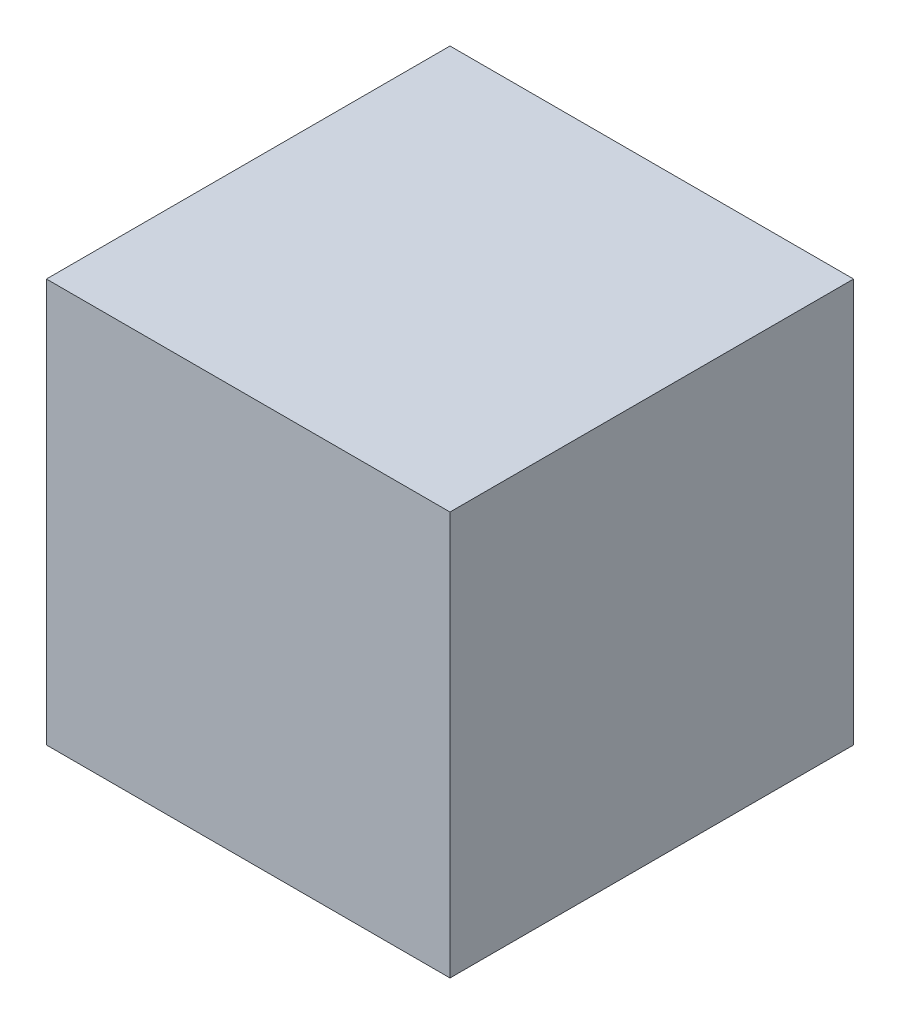
SolidWorks part; units mm, degrees
ref_plane "Front Plane" through (0, 0, 0) normal (0, 0, 1) x (1, 0, 0)
ref_plane "Top Plane" through (0, 0, 0) normal (0, 1, 0) x (1, 0, 0)
ref_plane "Right Plane" through (0, 0, 0) normal (1, 0, 0) x (0, 0, -1)
sketch "Sketch1" plane through (0, 0, 0) normal (0, 1, 0) x (1, 0, 0)
  line L1 (0, 0) -> (914.4, 0)
  line L2 (0, 0) -> (0, -914.4)
  line L3 (0, -914.4) -> (914.4, -914.4)
  line L4 (914.4, 0) -> (914.4, -914.4)
extrude "Boss-Extrude1" add sketch "Sketch1" along normal blind 914.4
